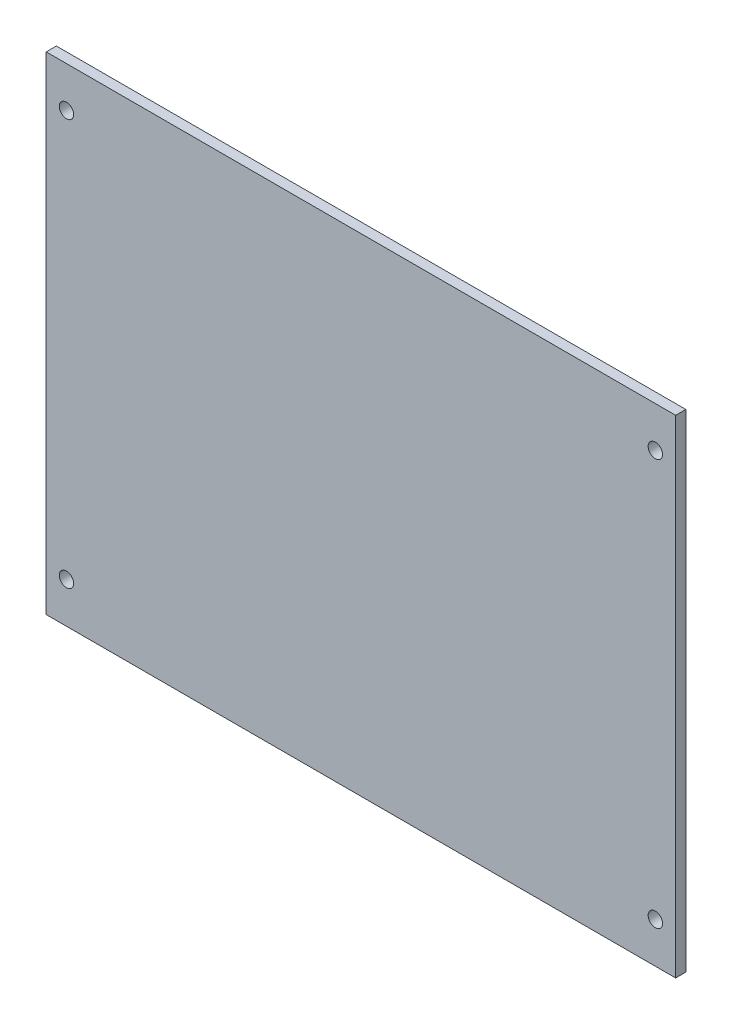
SolidWorks part; units mm, degrees
ref_plane "Front Plane" through (0, 0, 0) normal (0, 0, 1) x (1, 0, 0)
ref_plane "Top Plane" through (0, 0, 0) normal (0, 1, 0) x (1, 0, 0)
ref_plane "Right Plane" through (0, 0, 0) normal (1, 0, 0) x (0, 0, -1)
sketch "Sketch1" plane through (0, 0, 0) normal (0, 0, 1) x (1, 0, 0)
  line L1 (98.425, -76.2) -> (-98.425, -76.2)
  line L2 (98.425, -76.2) -> (98.425, 76.2)
  line L3 (98.425, 76.2) -> (-98.425, 76.2)
  line L4 (-98.425, -76.2) -> (-98.425, 76.2)
  line L5 (98.425, -76.2) -> (-98.425, 76.2) construction
  line L6 (98.425, 76.2) -> (-98.425, -76.2) construction
  line L7 (92.075, -63.5) -> (-92.075, -63.5) construction
  line L8 (92.075, -63.5) -> (92.075, 63.5) construction
  line L9 (92.075, 63.5) -> (-92.075, 63.5) construction
  line L10 (-92.075, -63.5) -> (-92.075, 63.5) construction
  line L11 (92.075, -63.5) -> (-92.075, 63.5) construction
  line L12 (92.075, 63.5) -> (-92.075, -63.5) construction
  circle A0 centre (-92.075, 63.5) radius 2.25
  circle A1 centre (92.075, 63.5) radius 2.25
  circle A2 centre (92.075, -63.5) radius 2.25
  circle A3 centre (-92.075, -63.5) radius 2.25
  point P0 (0, 0)
  point P6 (0, 0)
  point P13 (92.6933, -63.5)
  point P14 (0, 0)
  dimension "D5" = 4.5
  dimension "D1" = 196.85
  dimension "D2" = 152.4
  dimension "D3" = 6.35
  dimension "D4" = 12.7
  dimension "D6" = 2
  dimension "D7" = 2
extrude "Boss-Extrude1" add sketch "Sketch1" along normal blind 3.175
